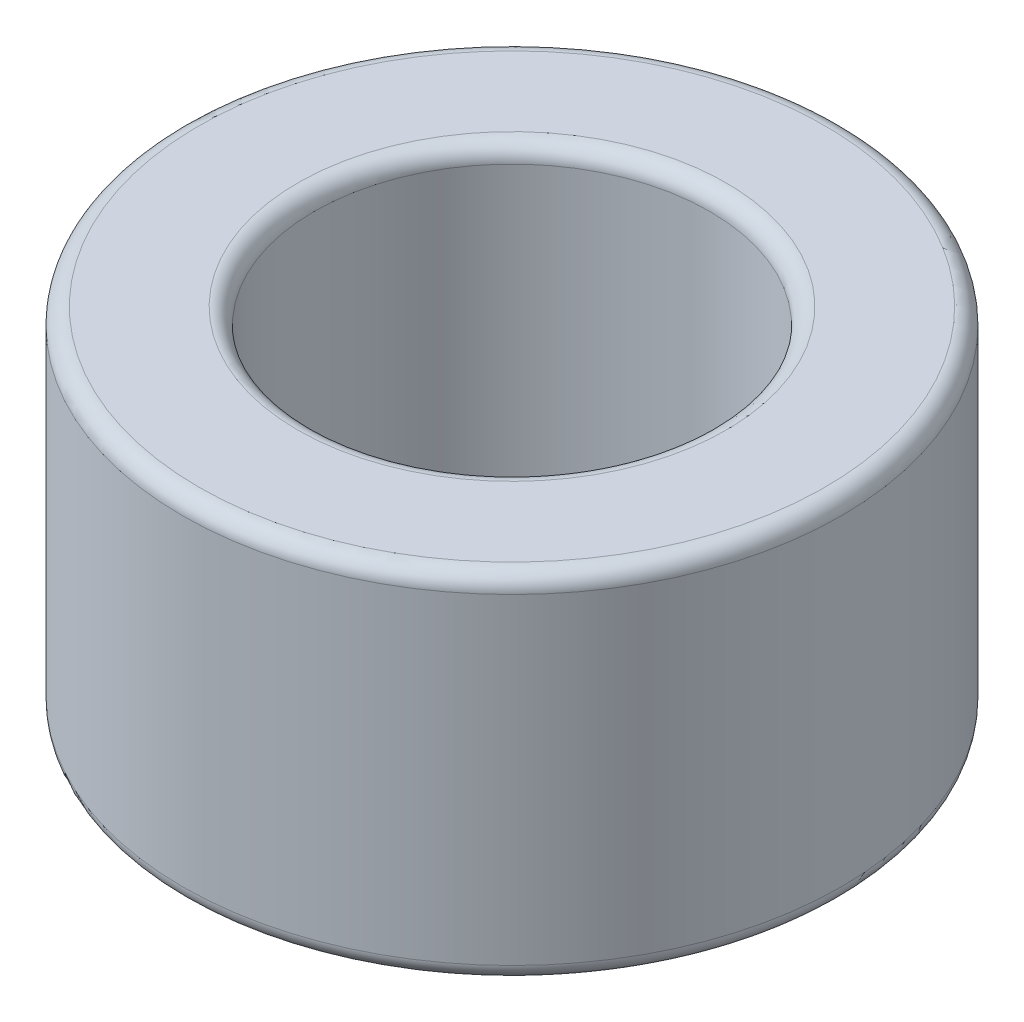
SolidWorks part; units mm, degrees
ref_plane "Front Plane" through (0, 0, 0) normal (0, 0, 1) x (1, 0, 0)
ref_plane "Top Plane" through (0, 0, 0) normal (0, 1, 0) x (1, 0, 0)
ref_plane "Right Plane" through (0, 0, 0) normal (1, 0, 0) x (0, 0, -1)
sketch "Sketch1" plane through (0, 0, 0) normal (0, 1, 0) x (1, 0, 0)
  circle A0 centre (0, 0) radius 4
  circle A1 centre (0, 0) radius 2.4
  dimension "D1" = 8
  dimension "D2" = 4.8
extrude "Boss-Extrude1" add sketch "Sketch1" along normal blind 4.3
fillet "Fillet1" radius 0.2 4 edges at (0, 0, 2.4) (0, 0, 4) (0, 4.3, 2.4) (0, 4.3, 4)
